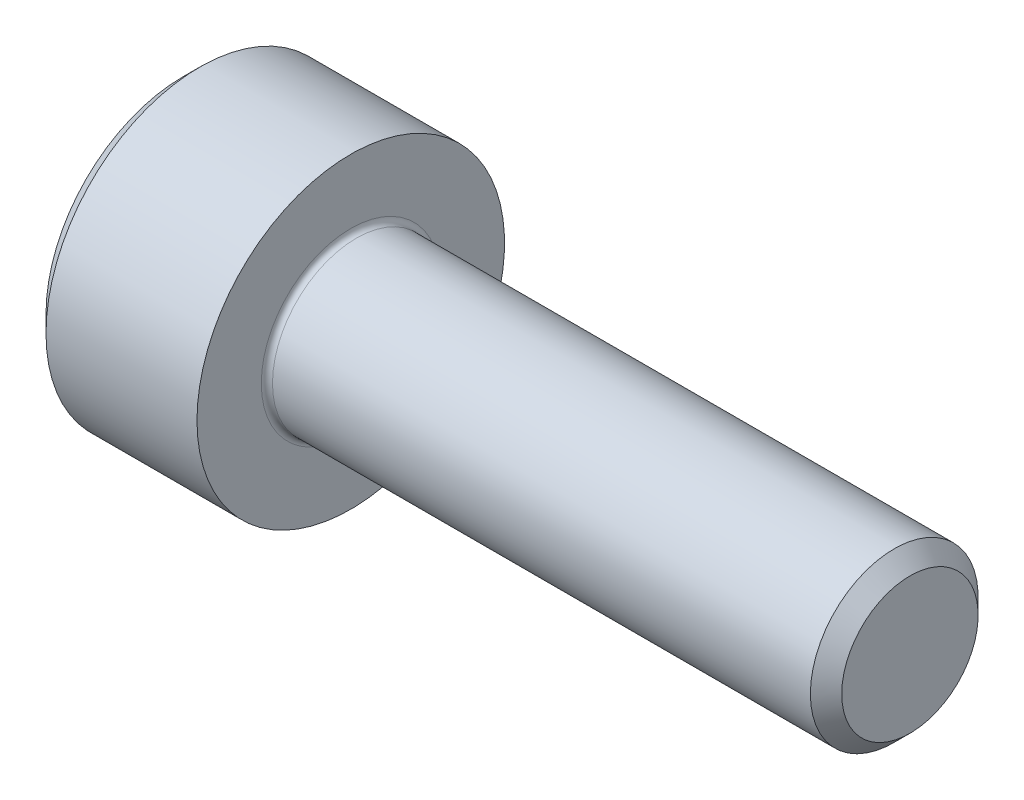
SolidWorks part; units mm, degrees
revolve "Base-Revolve" add sketch "BodySke"
sketch "BodySke" plane through (0, 0, 0) normal (0, 0, 1) x (1, 0, 0)
  line L0 (0, 0) -> (0, 2.45)
  line L1 (0.3, 2.75) -> (3, 2.75)
  line L2 (3, 2.75) -> (3, 1.5)
  line L3 (3, 1.5) -> (12.7195, 1.5)
  line L4 (13, 1.2195) -> (13, 0)
  line L5 (13, 0) -> (0, 0)
  line L6 (-31.75, 0) -> (127, 0) construction
  line L7 (0, 2.45) -> (0.3, 2.75)
  line L8 (13, 1.2195) -> (12.7195, 1.5)
  line L9 (0, -2.45) -> (0.3, -2.75) construction
  line L10 (13, -1.2195) -> (12.7195, -1.5) construction
  line L11 (3.5, 0.3925) -> (3.5, -5.9575) construction
  line L12 (3, 0.3925) -> (3, -5.9575) construction
  line L13 (-37, 0.3925) -> (-37, -5.9575) construction
  dimension "Diameter" = 3
  dimension "Head_ht" = 3
  dimension "Length" = 10
  dimension "Body_ch_ang" = 45
  dimension "Head_dia" = 5.5
  dimension "Head_ch_ang" = 45
  dimension "Minor_dia" = 2.439
  dimension "Advance" = 0.5
  dimension "Thread_nom" = 10
  dimension "Thread_length" = 50
  dimension "Head_ch_ht" = 0.3
cosmetic thread "ThreadCosmetic" [suppressed]
fillet "Fillet1" radius 0.1 1 edges at (3, 0, 1.5)
ref_plane "Plane1" through (0, 0, 0) normal (0, 0, 1) x (1, 0, 0)
ref_plane "Plane2" through (0, 0, 0) normal (0, 1, 0) x (1, 0, 0)
ref_plane "Plane3" through (0, 0, 0) normal (1, 0, 0) x (0, 0, -1)
other "Configuration Table"
sketch "Sketch2" plane through (0, 0, 0) normal (0, 0, 1) x (1, 0, 0)
  line L0 (0, 1.28) -> (1.3, 1.28)
  line L1 (1.3, 1.28) -> (2.039, 0)
  line L2 (-31.75, 0) -> (127, 0) construction
  line L3 (2.039, 0) -> (0, 0)
  line L4 (0, 0) -> (0, 1.28)
  line L5 (0, 2.45) -> (0, -2.45) construction
  line L6 (0, 0) -> (47.625, 0) construction
  line L7 (3, -2.75) -> (3, 2.75) construction
  dimension "D1" = 1.28
  dimension "D2" = 60
revolve "Hex-PreBroach" cut sketch "Sketch2" angle 360 about L6
sketch "Sketch3" plane through (0, 0, 0) normal (-1, 0, 0) x (0, 0.5, 0.866)
  line L0 (0.739, 1.28) -> (-0.739, 1.28)
  line L1 (-0.739, 1.28) -> (-1.478, 0)
  line L2 (0.739, 1.28) -> (1.478, 0)
  line L3 (0.739, -1.28) -> (1.478, 0)
  line L4 (0.739, -1.28) -> (-0.739, -1.28)
  line L5 (-0.739, -1.28) -> (-1.478, 0)
  dimension "D1" = 1.28
  dimension "D2" = 1.28
  dimension "Hex_size" = 2.56
extrude "Hex" cut sketch "Sketch3" against normal blind 1.3
sketch "Sketch4" plane through (0, 0, 0) normal (-1, 0, 0) x (0, 0, 1)
  line L0 (0, 0) -> (1.4605, 0)
  line L1 (0, 0) -> (6.1484, 3.5498) construction
  line L2 (0, 0) -> (0.7302, 1.2648)
  line L3 (1.2009, 0.3267) -> (1.3933, 0.4378)
  line L4 (0.8834, 0.8767) -> (1.0758, 0.9877)
  arc A0 (1.2009, 0.3267) -> (0.8834, 0.8767) centre (0, 0) ccw
  arc A1 (1.4605, 0) -> (1.3933, 0.4378) centre (0, 0) ccw
  arc A2 (0.7302, 1.2648) -> (1.0758, 0.9877) centre (0, 0) cw
  dimension "D1" = 30
  dimension "D2" = 60
  dimension "Spline_p_dim" = 0.635
  dimension "D3" = 0.3175
extrude "Spline" [suppressed] cut sketch "Sketch4" against normal blind 1.3
pattern_circular "CirPattern1" [suppressed] count 6 every 60
sketch "Sketch5" plane through (0, 0, 0) normal (0, 0, 1) x (1, 0, 0)
  line L0 (-31.75, 0) -> (127, 0) construction
  line L2 (0, 2.45) -> (0, -2.45) construction
  circle A0 centre (1.2, 0) radius 0.475
  dimension "Drilled_hole_dia" = 0.95
  dimension "Drilled_hole_loc" = 1.2
extrude "Hole" [suppressed] cut sketch "Sketch5" against normal through all and the other way through all
pattern_circular "Drilled-4" [suppressed] count 2 every 60
pattern_circular "Drilled-6" [suppressed] count 3 every 60
sketch "ThdSchSke" plane through (0, 0, 0) normal (0, 0, 1) x (1, 0, 0)
  line L0 (3.5, -1.2195) -> (3.3036, -1.5)
  line L1 (3.5, -1.2195) -> (3.6964, -1.5)
  line L2 (3.6964, -1.5) -> (3.6964, -1.875)
  line L3 (-3.175, 0) -> (5.1513, 0) construction
  line L5 (3.6964, -1.875) -> (3.3036, -1.875)
  line L6 (3.3036, -1.875) -> (3.3036, -1.5)
  line L7 (0, 2.45) -> (0, -2.45) construction
  dimension "Thread_minor" = 2.439
  dimension "Diameter" = 3
  dimension "Start" = 3.5
revolve "ThreadSchematic" [suppressed] cut sketch "ThdSchSke" angle 360 about L3
pattern_linear "ThdSchPat" [suppressed]
equation "\"D2@Sketch3\" = \"Hex_size@Sketch3\" / 2"
equation "\"D1@Sketch3\" = \"Hex_size@Sketch3\" / 2"
equation "\"D1@Sketch2\" = \"Hex_size@Sketch3\" / 2"
equation "\"D3@Sketch4\" = \"Spline_p_dim@Sketch4\" / 2"
equation "\"Thread_minor@ThreadCosmetic\"  =  \"Minor_dia@BodySke\""
equation "\"D2@CirPattern1\" = 360 / \"Num_teeth@CirPattern1\""
equation "\"Wall_thickness@Sketch2\" = \"Head_ht@BodySke\" - \"Key_eng@Hex\""
equation "\"Thread_length@ThreadCosmetic\" = ((sgn( (\"Length@BodySke\" - \"Advance@BodySke\" ) - \"Thread_nom@BodySke\" )-1)*( (\"Length@BodySke\" - \"Advance@BodySke\" ) - \"Thread_nom@BodySke\" ))/-2+ \"Thread_nom@BodySke\""
equation "\"Thread_minor@ThdSchSke\" = \"Minor_dia@BodySke\""
equation "\"Diameter@ThdSchSke\" = \"Diameter@BodySke\""
equation "\"Overcut@ThdSchSke\" = \"Diameter@BodySke\" * 1.25"
equation "\"Start@ThdSchSke\" = \"Head_ht@BodySke\" + \"Length@BodySke\" - \"Thread_length@ThreadCosmetic\"  '---Non-countersunk---"
equation "\"Num_threads@ThdSchPat\" = int( \"Thread_length@ThreadCosmetic\" / \"Advance@BodySke\" + 0.999 )  + 1"
equation "\"Advance@ThdSchPat\" = \"Thread_length@ThreadCosmetic\" /  (\"Num_threads@ThdSchPat\" - 1) 'relax it"
equation "\"Num_threads@ThdSchPat\" = \"Num_threads@ThdSchPat\" - sgn( \"Num_threads@ThdSchPat\" - 1) '---chamfered tips only---"
